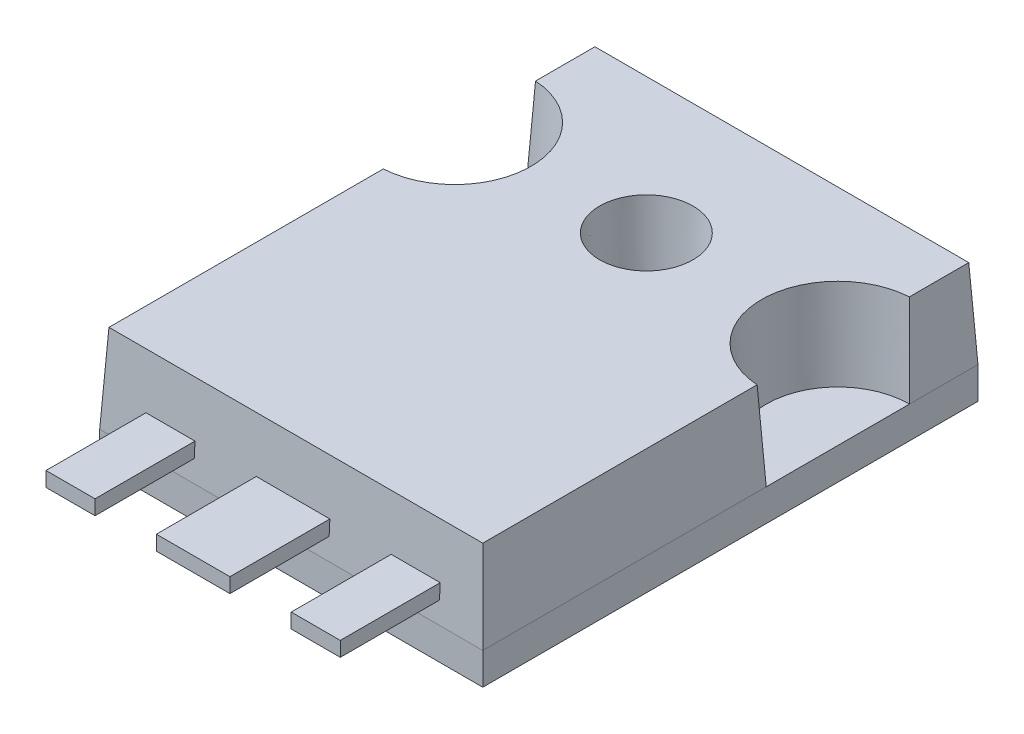
SolidWorks part; units mm, degrees
ref_plane "Front Plane" through (0, 0, 0) normal (0, 0, 1) x (1, 0, 0)
ref_plane "Top Plane" through (0, 0, 0) normal (0, 1, 0) x (1, 0, 0)
ref_plane "Right Plane" through (0, 0, 0) normal (1, 0, 0) x (0, 0, -1)
sketch "Sketch1" plane through (0, 0, 0) normal (0, 1, 0) x (1, 0, 0)
  line L0 (7.8105, 14.4785) -> (7.8105, 20.193) construction
  line L1 (0, 0) -> (15.621, 0)
  line L2 (0, 0) -> (0, 20.193)
  line L3 (0, 20.193) -> (15.621, 20.193)
  line L4 (15.621, 0) -> (15.621, 20.193)
  circle A0 centre (7.8105, 14.4785) radius 1.7145
  point P7 (7.8105, 16.193)
  point P8 (6.096, 14.4785)
  dimension "D1" = 15.621
  dimension "D3" = 3.429
  dimension "D2" = 20.193
  dimension "D4" = 4
extrude "Boss-Extrude1" add sketch "Sketch1" along normal blind 1.3
sketch "Sketch2" plane through (0, 1.3, 0) normal (0, 1, 0) x (1, 0, 0)
  line L0 (0, 14.4785) -> (15.621, 14.4785) construction
  line L1 (15.621, 0) -> (15.621, 20.193) construction
  line L4 (0, 20.193) -> (0, 0)
  line L5 (0, 0) -> (15.621, 0)
  line L6 (15.621, 0) -> (15.621, 20.193)
  line L7 (15.621, 20.193) -> (0, 20.193)
  line L8 (0, 20.193) -> (0, 0)
  line L9 (0, 0) -> (15.621, 0)
  line L10 (15.621, 0) -> (15.621, 20.193)
  line L11 (15.621, 20.193) -> (0, 20.193)
  circle A0 centre (15.621, 14.4785) radius 2.921
  circle A1 centre (7.8105, 14.4785) radius 1.7145
  circle A2 centre (7.8105, 14.4785) radius 1.7145
  circle A3 centre (0, 14.4785) radius 2.921
  point P11 (7.8105, 14.4785)
  line M7 (0, 20.193) -> (0, 0)
  line M8 (0, 0) -> (15.621, 0)
  line M9 (15.621, 0) -> (15.621, 20.193)
  line M10 (15.621, 20.193) -> (0, 20.193)
  circle M11 centre (7.8105, 14.4785) radius 1.7145
  dimension "D3" = 5.842
  dimension "D4" = 5.842
  dimension "D1" = 0
  dimension "D2" = 0
extrude "Boss-Extrude2" add sketch "Sketch2" along normal blind 3.6 draft 3 contours A3 L0 A0 M11 M9 M10 M7 | L0 A3 A0 A2 M7 M8 M9
ref_plane "Plane1" through (0, 2.45, 0) normal (0, 1, 0) x (1, 0, 0)
sketch "Sketch3" plane through (0, 2.45, 0) normal (0, 1, 0) x (1, 0, 0)
  line L0 (0, 0) -> (15.621, 0) construction
  line L1 (0, 0) -> (15.621, 0)
  line L2 (7.8105, -4) -> (7.8105, 0) construction
  line L3 (1.8105, 0) -> (3.8105, 0)
  line L4 (1.8105, 0) -> (1.8105, -4)
  line L5 (1.8105, -4) -> (3.8105, -4)
  line L6 (3.8105, 0) -> (3.8105, -4)
  line L7 (13.8105, 0) -> (11.8105, 0)
  line L8 (13.8105, 0) -> (13.8105, -4)
  line L9 (13.8105, -4) -> (11.8105, -4)
  line L10 (11.8105, 0) -> (11.8105, -4)
  line L11 (9.3105, 0) -> (6.3105, 0)
  line L12 (9.3105, 0) -> (9.3105, -4)
  line L13 (9.3105, -4) -> (6.3105, -4)
  line L14 (6.3105, 0) -> (6.3105, -4)
  line L16 (1.8105, 0) -> (3.8105, 0)
  line L17 (1.8105, 0) -> (1.8105, 2.1553)
  line L18 (1.8105, 2.1553) -> (3.8105, 2.1553)
  line L19 (3.8105, 0) -> (3.8105, 2.1553)
  line L20 (6.3105, 0) -> (7.8105, 0)
  line L21 (6.3105, 0) -> (6.3105, 2.9988)
  line L22 (6.3105, 2.9988) -> (7.8105, 2.9988)
  line L23 (7.8105, 0) -> (7.8105, 2.9988)
  line L24 (11.8105, 0) -> (13.8105, 0)
  line L25 (11.8105, 0) -> (11.8105, 2.1553)
  line L26 (11.8105, 2.1553) -> (13.8105, 2.1553)
  line L27 (13.8105, 0) -> (13.8105, 2.1553)
  line L28 (9.3105, 0) -> (7.8105, 0)
  line L29 (9.3105, 0) -> (9.3105, 2.9988)
  line L30 (9.3105, 2.9988) -> (7.8105, 2.9988)
  line L31 (7.8105, 0) -> (7.8105, 2.9988)
  dimension "D1" = 2
  dimension "D2" = 2
  dimension "D3" = 3
  dimension "D4" = 2.5
  dimension "D5" = 2.5
  dimension "D6" = 4
  dimension "D7" = 4
  dimension "D8" = 4
extrude "Boss-Extrude3" add sketch "Sketch3" along normal blind 0.3 and the other way blind 0.3 contours L1 L19 L18 L17 | L6 L1 L4 L5 | L1 L23 L22 L21 | L29 L30 L23 L11 | L13 L2 L1 L14 | L2 L13 L12 L11 | L1 L27 L26 L25 | L1 L10 L9 L8
